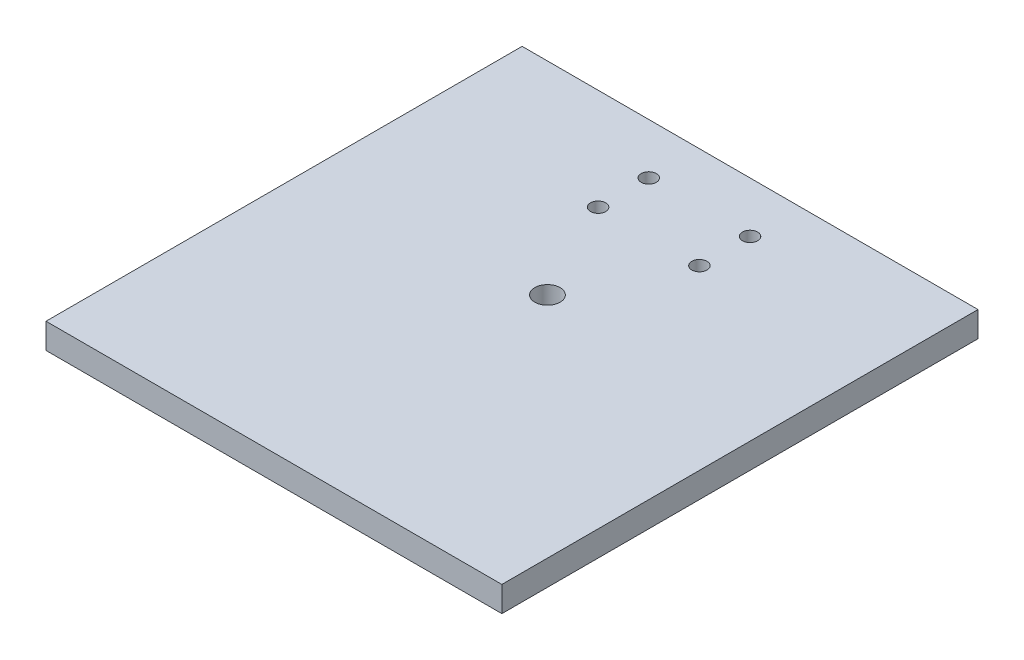
SolidWorks part; units mm, degrees
ref_plane "Front Plane" through (0, 0, 0) normal (0, 0, 1) x (1, 0, 0)
ref_plane "Top Plane" through (0, 0, 0) normal (0, 1, 0) x (1, 0, 0)
ref_plane "Right Plane" through (0, 0, 0) normal (1, 0, 0) x (0, 0, -1)
sketch "Sketch1" plane through (0, 0, 0) normal (0, 1, 0) x (1, 0, 0)
  line L0 (44.45, 106.68) -> (69.85, 106.68) construction
  line L1 (0, 0) -> (114.3, 0)
  line L2 (0, 0) -> (0, 119.38)
  line L3 (0, 119.38) -> (114.3, 119.38)
  line L4 (114.3, 0) -> (114.3, 119.38)
  line L21 (69.85, 106.68) -> (69.85, 93.98) construction
  line L22 (69.85, 93.98) -> (44.45, 93.98) construction
  line L23 (44.45, 93.98) -> (44.45, 106.68) construction
  circle A4 centre (44.45, 106.68) radius 1.905
  circle A5 centre (69.85, 106.68) radius 1.905
  circle A6 centre (44.45, 93.98) radius 1.905
  circle A7 centre (69.85, 93.98) radius 1.905
  circle A8 centre (57.15, 68.58) radius 3.175
  point P7 (0, 0)
  point P35 (57.15, 119.38)
  point P36 (57.15, 106.68)
  dimension "D8" = 3.81
  dimension "D3" = 6.35
  dimension "D1" = 114.3
  dimension "D2" = 119.38
  dimension "D4" = 25.4
  dimension "D9" = 25.4
  dimension "D10" = 12.7
  dimension "D11" = 12.7
extrude "Boss-Extrude1" add sketch "Sketch1" along normal blind 6.35
